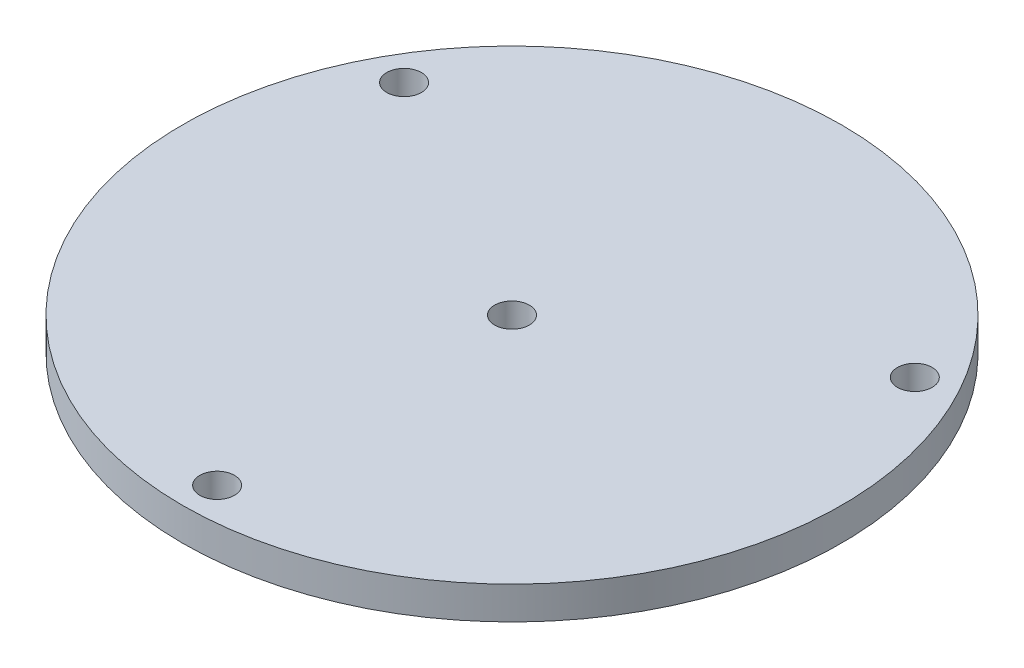
SolidWorks part; units mm, degrees
ref_plane "Front Plane" through (0, 0, 0) normal (0, 0, 1) x (1, 0, 0)
ref_plane "Top Plane" through (0, 0, 0) normal (0, 1, 0) x (1, 0, 0)
ref_plane "Right Plane" through (0, 0, 0) normal (1, 0, 0) x (0, 0, -1)
sketch "Sketch1" plane through (0, 0, 0) normal (0, 1, 0) x (1, 0, 0)
  line L0 (0, -47.6504) -> (0, -60.3504) construction
  circle A0 centre (0, 0) radius 60.3504
  circle A1 centre (0, 0) radius 3.175
  circle A2 centre (0, -54.0004) radius 3.175
  circle A3 centre (-46.7657, 27.0002) radius 3.175
  circle A4 centre (46.7657, 27.0002) radius 3.175
  point P14 (0, 0)
  dimension "D1" = 120.7008
  dimension "D2" = 6.35
  dimension "D3" = 6.35
  dimension "D5" = 3
extrude "Boss-Extrude1" add sketch "Sketch1" along normal blind 6 contours A1
